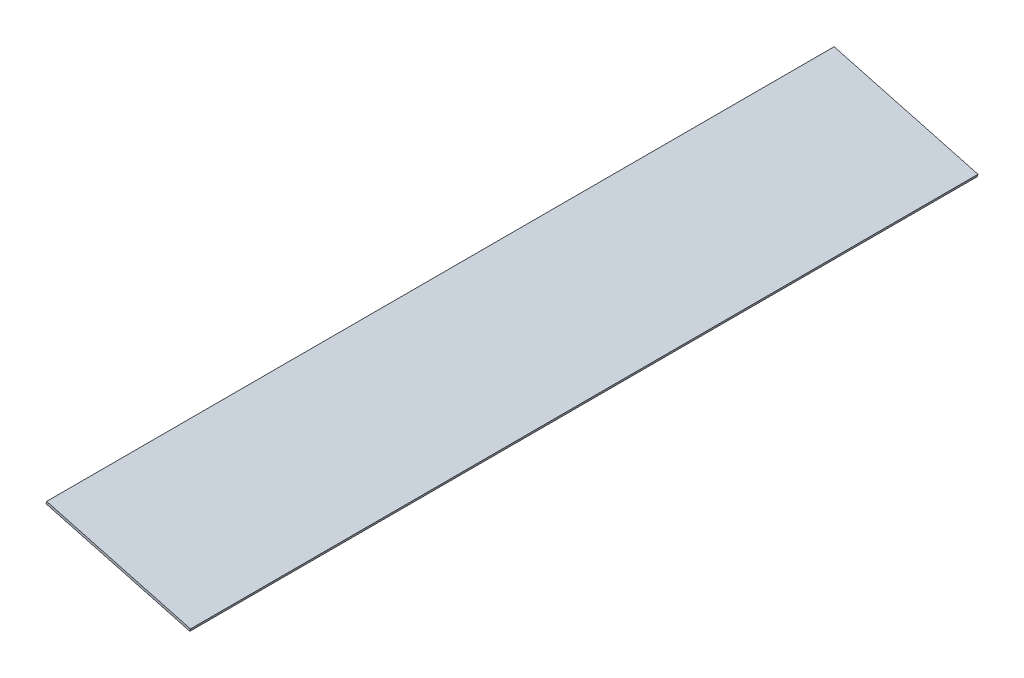
SolidWorks part; units mm, degrees
material "6061-T6 (SS)"
ref_plane "Front Plane" through (0, 0, 0) normal (0, 0, 1) x (1, 0, 0)
ref_plane "Top Plane" through (0, 0, 0) normal (0, 1, 0) x (1, 0, 0)
ref_plane "Right Plane" through (0, 0, 0) normal (1, 0, 0) x (0, 0, -1)
sketch "Sketch1" plane through (0, 0, 0) normal (0, 0, 1) x (1, 0, 0)
  line L0 (0, 0) -> (-100.076, 0) construction
  line L1 (0, 0) -> (-93.3722, 25.019)
  line L2 (0, 0) -> (0.4109, 1.5334)
  line L3 (0.4109, 1.5334) -> (-92.9613, 26.5524)
  line L4 (-92.9613, 26.5524) -> (-93.3722, 25.019)
  dimension "D1" = 100.076
  dimension "D2" = 15
  dimension "D3" = 1.5875
extrude "Boss-Extrude1" add sketch "Sketch1" along normal blind 511.175
